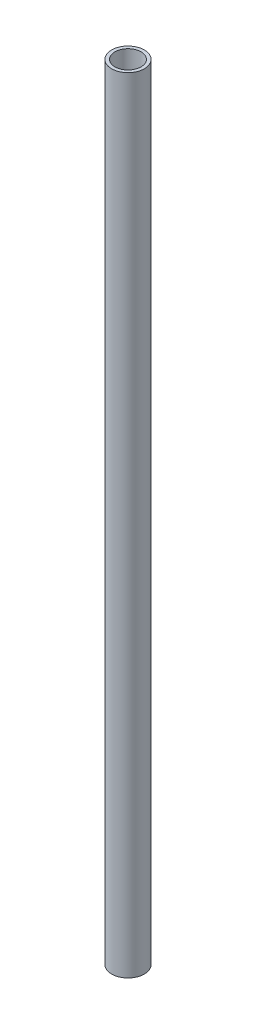
SolidWorks part; units mm, degrees
material "Carbon Fibre"
ref_plane "Front Plane" through (0, 0, 0) normal (0, 0, 1) x (1, 0, 0)
ref_plane "Top Plane" through (0, 0, 0) normal (0, 1, 0) x (1, 0, 0)
ref_plane "Right Plane" through (0, 0, 0) normal (1, 0, 0) x (0, 0, -1)
sketch "Sketch1" plane through (0, 0, 0) normal (0, 1, 0) x (1, 0, 0)
  circle A0 centre (0, 0) radius 5
  circle A1 centre (0, 0) radius 4
  dimension "D1" = 10
  dimension "D2" = 8
extrude "Boss-Extrude1" add sketch "Sketch1" along normal mid plane 240
